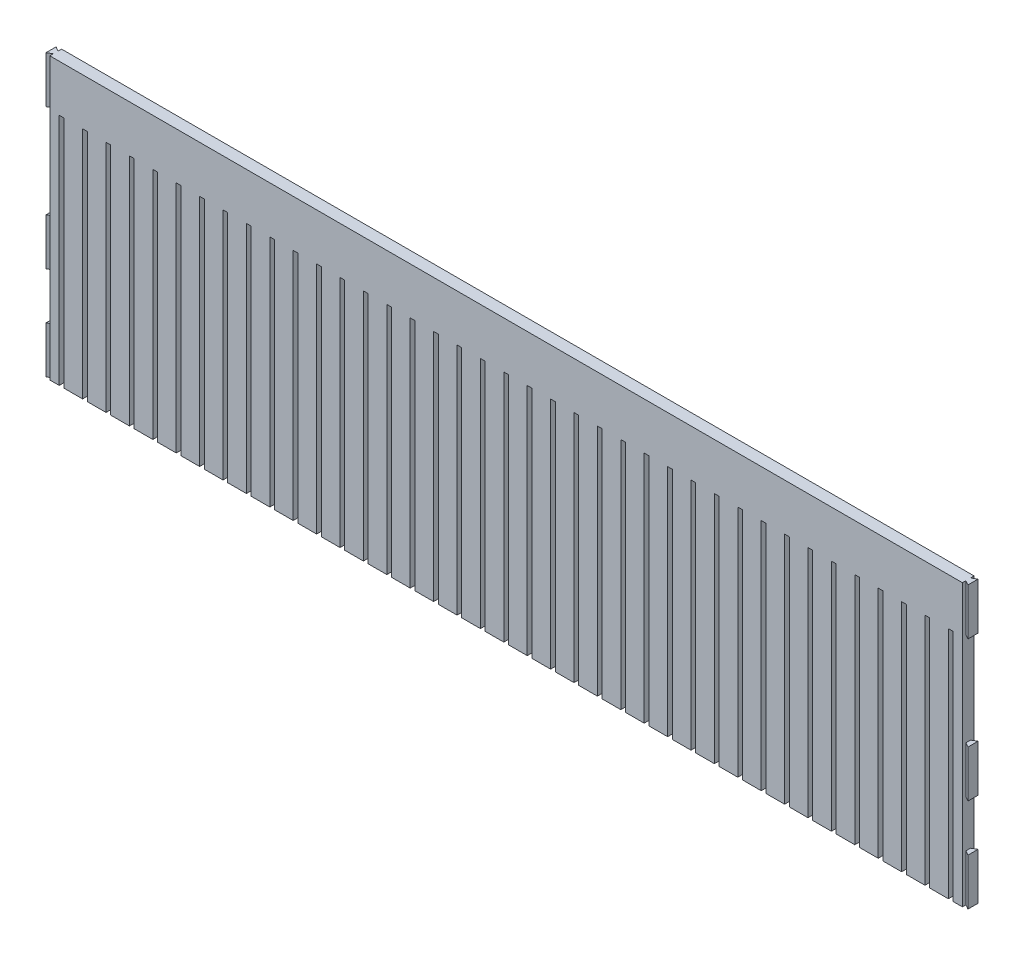
SolidWorks part; units mm, degrees
ref_plane "前视基准面" through (0, 0, 0) normal (0, 0, 1) x (1, 0, 0)
ref_plane "上视基准面" through (0, 0, 0) normal (0, 1, 0) x (1, 0, 0)
ref_plane "右视基准面" through (0, 0, 0) normal (1, 0, 0) x (0, 0, -1)
sketch "草图1" plane through (0, 0, 0) normal (0, 0, 1) x (1, 0, 0)
  line L1 (-180, 40) -> (180, 40)
  line L2 (-180, 40) -> (-180, -40)
  line L3 (-180, -40) -> (180, -40)
  line L4 (180, 40) -> (180, -40)
  line L5 (-180, 40) -> (180, -40) construction
  line L6 (-180, -40) -> (180, 40) construction
  point P0 (0, 0)
  dimension "D1" = 80
  dimension "D2" = 360
extrude "凸台-拉伸1" add sketch "草图1" along normal blind 5
sketch "草图3" plane through (0, -40, 0) normal (0, -1, 0) x (1, 0, 0)
  line L1 (-180, 5) -> (180, 5)
  line L2 (-180, 5) -> (-180, 0)
  line L3 (-180, 0) -> (180, 0)
  line L4 (180, 5) -> (180, 0)
extrude "凸台-拉伸2" add sketch "草图3" along normal blind 40
sketch "草图4" plane through (-180, 0, 0) normal (-1, 0, 0) x (0, 0, 1)
  line L1 (0, 40) -> (5, 40)
  line L2 (0, 40) -> (0, -80)
  line L3 (0, -80) -> (5, -80)
  line L4 (5, 40) -> (5, -80)
extrude "凸台-拉伸3" add sketch "草图4" along normal blind 15
sketch "草图5" plane through (180, 0, 0) normal (1, 0, 0) x (0, 0, -1)
  line L0 (0, -80) -> (0, 40) construction
  line L1 (-5, 40) -> (0, 40)
  line L2 (-5, 40) -> (-5, -80)
  line L3 (-5, -80) -> (0, -80)
  line L4 (0, 40) -> (0, -80)
extrude "凸台-拉伸4" add sketch "草图5" along normal blind 15
sketch "草图6" plane through (0, -80, 0) normal (0, -1, 0) x (1, 0, 0)
  line L0 (-195, 3.5) -> (-197, 4.6547)
  line L1 (-195, 0) -> (-195, 5) construction
  line L2 (-197, 4.6547) -> (-197, 0.3453)
  line L3 (-197, 0.3453) -> (-195, 1.5)
  line L4 (-195, 1.5) -> (-195, 3.5)
  line L5 (195, 5) -> (-195, 5) construction
  line L6 (0, -1000) -> (0, 49000) construction
  line L7 (195, 1.5) -> (195, 3.5)
  line L8 (197, 0.3453) -> (195, 1.5)
  line L9 (197, 4.6547) -> (197, 0.3453)
  line L10 (195, 3.5) -> (197, 4.6547)
  point P4 (-195, 2.5)
  dimension "D1" = 2
  dimension "D2" = 60
  dimension "D3" = 60
  dimension "D4" = 1.5
  dimension "D5" = 1.5
extrude "凸台-拉伸5" add sketch "草图6" against normal blind 20
sketch "草图7" plane through (0, 40, 0) normal (0, 1, 0) x (1, 0, 0)
  line L4 (-195, -3.5) -> (-195, -1.5)
  line L5 (-195, -1.5) -> (-197, -0.3453)
  line L6 (-197, -0.3453) -> (-197, -4.6547)
  line L7 (-197, -4.6547) -> (-195, -3.5)
  line L8 (-195, -3.5) -> (-195, -1.5)
  line L9 (-195, -1.5) -> (-197, -0.3453)
  line L10 (-197, -0.3453) -> (-197, -4.6547)
  line L11 (-197, -4.6547) -> (-195, -3.5)
  line L12 (197, -0.3453) -> (195, -1.5)
  line L13 (195, -1.5) -> (195, -3.5)
  line L14 (195, -3.5) -> (197, -4.6547)
  line L15 (197, -4.6547) -> (197, -0.3453)
  line L16 (197, -0.3453) -> (195, -1.5)
  line L17 (195, -1.5) -> (195, -3.5)
  line L18 (195, -3.5) -> (197, -4.6547)
  line L19 (197, -4.6547) -> (197, -0.3453)
  dimension "D1" = 0
  dimension "D2" = 0
extrude "凸台-拉伸6" add sketch "草图7" against normal blind 20
sketch "草图8" plane through (0, 0, 0) normal (0, 1, 0) x (1, 0, 0)
  line L4 (-195, -3.5) -> (-195, -1.5)
  line L5 (-195, -1.5) -> (-197, -0.3453)
  line L6 (-197, -0.3453) -> (-197, -4.6547)
  line L7 (-197, -4.6547) -> (-195, -3.5)
  line L8 (-195, -3.5) -> (-195, -1.5)
  line L9 (-195, -1.5) -> (-197, -0.3453)
  line L10 (-197, -0.3453) -> (-197, -4.6547)
  line L11 (-197, -4.6547) -> (-195, -3.5)
  line L12 (197, -0.3453) -> (195, -1.5)
  line L13 (195, -1.5) -> (195, -3.5)
  line L14 (195, -3.5) -> (197, -4.6547)
  line L15 (197, -4.6547) -> (197, -0.3453)
  line L16 (197, -0.3453) -> (195, -1.5)
  line L17 (195, -1.5) -> (195, -3.5)
  line L18 (195, -3.5) -> (197, -4.6547)
  line L19 (197, -4.6547) -> (197, -0.3453)
  dimension "D1" = 0
  dimension "D2" = 0
extrude "凸台-拉伸7" add sketch "草图8" against normal blind 20 from offset 20 offset against normal yes
sketch "草图9" plane through (0, -80, 0) normal (0, -1, 0) x (1, 0, 0)
  line L0 (195, 5) -> (-195, 5) construction
  line L1 (9, 5) -> (11, 5)
  line L2 (9, 5) -> (9, 0)
  line L3 (9, 0) -> (11, 0)
  line L4 (11, 5) -> (11, 0)
  line L5 (-195, 0) -> (195, 0) construction
  line L6 (19, 5) -> (21, 5)
  line L7 (-1, 5) -> (1, 5)
  line L8 (-1, 5) -> (-1, 0)
  line L9 (-1, 0) -> (1, 0)
  line L10 (1, 5) -> (1, 0)
  line L11 (19, 5) -> (19, 0)
  line L12 (19, 0) -> (21, 0)
  line L13 (21, 5) -> (21, 0)
  line L14 (29, 5) -> (31, 5)
  line L15 (29, 5) -> (29, 0)
  line L16 (29, 0) -> (31, 0)
  line L17 (31, 5) -> (31, 0)
  line L18 (39, 5) -> (41, 5)
  line L19 (39, 5) -> (39, 0)
  line L20 (39, 0) -> (41, 0)
  line L21 (41, 5) -> (41, 0)
  line L22 (49, 5) -> (51, 5)
  line L23 (49, 5) -> (49, 0)
  line L24 (49, 0) -> (51, 0)
  line L25 (51, 5) -> (51, 0)
  line L26 (59, 5) -> (61, 5)
  line L27 (59, 5) -> (59, 0)
  line L28 (59, 0) -> (61, 0)
  line L29 (61, 5) -> (61, 0)
  line L30 (69, 5) -> (71, 5)
  line L31 (69, 5) -> (69, 0)
  line L32 (69, 0) -> (71, 0)
  line L33 (71, 5) -> (71, 0)
  line L34 (79, 5) -> (81, 5)
  line L35 (79, 5) -> (79, 0)
  line L36 (79, 0) -> (81, 0)
  line L37 (81, 5) -> (81, 0)
  line L38 (89, 5) -> (91, 5)
  line L39 (89, 5) -> (89, 0)
  line L40 (89, 0) -> (91, 0)
  line L41 (91, 5) -> (91, 0)
  line L42 (99, 5) -> (101, 5)
  line L43 (99, 5) -> (99, 0)
  line L44 (99, 0) -> (101, 0)
  line L45 (101, 5) -> (101, 0)
  line L46 (109, 5) -> (111, 5)
  line L47 (109, 5) -> (109, 0)
  line L48 (109, 0) -> (111, 0)
  line L49 (111, 5) -> (111, 0)
  line L50 (119, 5) -> (121, 5)
  line L51 (119, 5) -> (119, 0)
  line L52 (119, 0) -> (121, 0)
  line L53 (121, 5) -> (121, 0)
  line L54 (129, 5) -> (131, 5)
  line L55 (129, 5) -> (129, 0)
  line L56 (129, 0) -> (131, 0)
  line L57 (131, 5) -> (131, 0)
  line L58 (139, 5) -> (141, 5)
  line L59 (139, 5) -> (139, 0)
  line L60 (139, 0) -> (141, 0)
  line L61 (141, 5) -> (141, 0)
  line L62 (149, 5) -> (151, 5)
  line L63 (149, 5) -> (149, 0)
  line L64 (149, 0) -> (151, 0)
  line L65 (151, 5) -> (151, 0)
  line L66 (159, 5) -> (161, 5)
  line L67 (159, 5) -> (159, 0)
  line L68 (159, 0) -> (161, 0)
  line L69 (161, 5) -> (161, 0)
  line L70 (169, 5) -> (171, 5)
  line L71 (169, 5) -> (169, 0)
  line L72 (169, 0) -> (171, 0)
  line L73 (171, 5) -> (171, 0)
  line L74 (179, 5) -> (181, 5)
  line L75 (179, 5) -> (179, 0)
  line L76 (179, 0) -> (181, 0)
  line L77 (181, 5) -> (181, 0)
  line L78 (189, 5) -> (191, 5)
  line L79 (189, 5) -> (189, 0)
  line L80 (189, 0) -> (191, 0)
  line L81 (191, 5) -> (191, 0)
  line L82 (-11, 5) -> (-9, 5)
  line L83 (-11, 5) -> (-11, 0)
  line L84 (-11, 0) -> (-9, 0)
  line L85 (-9, 5) -> (-9, 0)
  line L86 (-21, 5) -> (-19, 5)
  line L87 (-21, 5) -> (-21, 0)
  line L88 (-21, 0) -> (-19, 0)
  line L89 (-19, 5) -> (-19, 0)
  line L90 (-31, 5) -> (-29, 5)
  line L91 (-31, 5) -> (-31, 0)
  line L92 (-31, 0) -> (-29, 0)
  line L93 (-29, 5) -> (-29, 0)
  line L94 (-41, 5) -> (-39, 5)
  line L95 (-41, 5) -> (-41, 0)
  line L96 (-41, 0) -> (-39, 0)
  line L97 (-39, 5) -> (-39, 0)
  line L98 (-51, 5) -> (-49, 5)
  line L99 (-51, 5) -> (-51, 0)
  line L100 (-51, 0) -> (-49, 0)
  line L101 (-49, 5) -> (-49, 0)
  line L102 (-61, 5) -> (-59, 5)
  line L103 (-61, 5) -> (-61, 0)
  line L104 (-61, 0) -> (-59, 0)
  line L105 (-59, 5) -> (-59, 0)
  line L106 (-71, 5) -> (-69, 5)
  line L107 (-71, 5) -> (-71, 0)
  line L108 (-71, 0) -> (-69, 0)
  line L109 (-69, 5) -> (-69, 0)
  line L110 (-81, 5) -> (-79, 5)
  line L111 (-81, 5) -> (-81, 0)
  line L112 (-81, 0) -> (-79, 0)
  line L113 (-79, 5) -> (-79, 0)
  line L114 (-91, 5) -> (-89, 5)
  line L115 (-91, 5) -> (-91, 0)
  line L116 (-91, 0) -> (-89, 0)
  line L117 (-89, 5) -> (-89, 0)
  line L118 (-101, 5) -> (-99, 5)
  line L119 (-101, 5) -> (-101, 0)
  line L120 (-101, 0) -> (-99, 0)
  line L121 (-99, 5) -> (-99, 0)
  line L122 (-111, 5) -> (-109, 5)
  line L123 (-111, 5) -> (-111, 0)
  line L124 (-111, 0) -> (-109, 0)
  line L125 (-109, 5) -> (-109, 0)
  line L126 (-121, 5) -> (-119, 5)
  line L127 (-121, 5) -> (-121, 0)
  line L128 (-121, 0) -> (-119, 0)
  line L129 (-119, 5) -> (-119, 0)
  line L130 (-131, 5) -> (-129, 5)
  line L131 (-131, 5) -> (-131, 0)
  line L132 (-131, 0) -> (-129, 0)
  line L133 (-129, 5) -> (-129, 0)
  line L134 (-141, 5) -> (-139, 5)
  line L135 (-141, 5) -> (-141, 0)
  line L136 (-141, 0) -> (-139, 0)
  line L137 (-139, 5) -> (-139, 0)
  line L138 (-151, 5) -> (-149, 5)
  line L139 (-151, 5) -> (-151, 0)
  line L140 (-151, 0) -> (-149, 0)
  line L141 (-149, 5) -> (-149, 0)
  line L142 (-161, 5) -> (-159, 5)
  line L143 (-161, 5) -> (-161, 0)
  line L144 (-161, 0) -> (-159, 0)
  line L145 (-159, 5) -> (-159, 0)
  line L146 (-171, 5) -> (-169, 5)
  line L147 (-171, 5) -> (-171, 0)
  line L148 (-171, 0) -> (-169, 0)
  line L149 (-169, 5) -> (-169, 0)
  line L150 (-181, 5) -> (-179, 5)
  line L151 (-181, 5) -> (-181, 0)
  line L152 (-181, 0) -> (-179, 0)
  line L153 (-179, 5) -> (-179, 0)
  line L154 (-191, 5) -> (-189, 5)
  line L155 (-191, 5) -> (-191, 0)
  line L156 (-191, 0) -> (-189, 0)
  line L157 (-189, 5) -> (-189, 0)
  point P0 (0, 0)
  dimension "D1" = 2
  dimension "D2" = 20
  dimension "D3" = 20
extrude "切除-拉伸1" cut sketch "草图9" against normal blind 100
